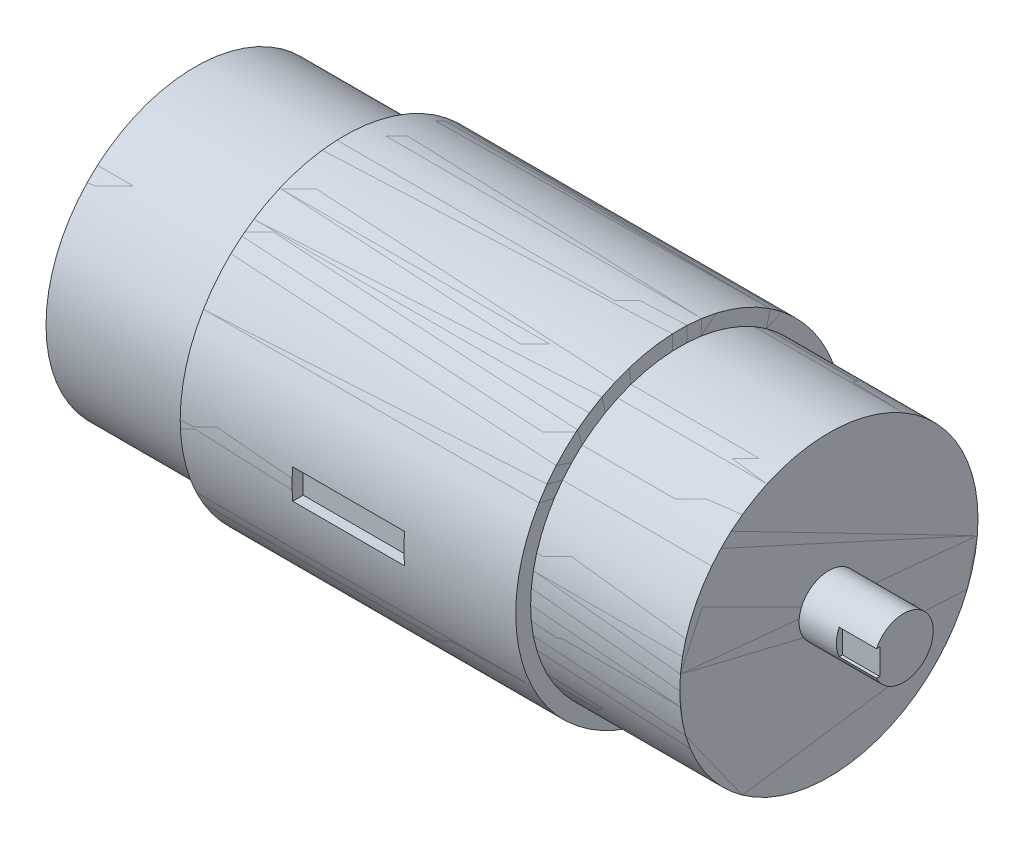
SolidWorks part; units mm, degrees
material "Cast Alloy Steel"
ref_plane "Front Plane" through (0, 0, 0) normal (0, 0, 1) x (1, 0, 0)
ref_plane "Top Plane" through (0, 0, 0) normal (0, 1, 0) x (1, 0, 0)
ref_plane "Right Plane" through (0, 0, 0) normal (1, 0, 0) x (0, 0, -1)
ref_plane "Plane1" through (800, 0, 0) normal (1, 0, 0) x (0, 0, -1)
sketch "Sketch3" plane through (800, 0, 0) normal (1, 0, 0) x (0, 0, -1)
  circle A0 centre (0, 0) radius 200
ref_plane "Plane2" through (200, 0, 0) normal (1, 0, 0) x (0, 0, -1)
ref_plane "Plane3" through (600, 0, 0) normal (1, 0, 0) x (0, 0, -1)
sketch "Sketch5" plane through (600, 0, 0) normal (1, 0, 0) x (0, 0, -1)
  circle A0 centre (0, 0) radius 220
  point P3 (-220, 0)
extrude "Boss-Extrude2" add sketch "Sketch3" against normal blind 200 contours A0
ref_plane "Plane4" through (800, 0, 0) normal (1, 0, 0) x (0, 0, -1)
sketch "Sketch6" plane through (800, 0, 0) normal (1, 0, 0) x (0, 0, -1)
  circle A0 centre (0, 0) radius 40
extrude "Boss-Extrude5" add sketch "Sketch6" along normal blind 100 separate body
ref_plane "Plane6" through (900, 0, 0) normal (1, 0, 0) x (0, 0, -1)
sketch "Sketch8" plane through (900, 0, 0) normal (1, 0, 0) x (0, 0, -1)
  line L3 (-36.1198, 17.186) -> (-31.7093, 17.186)
  line L5 (-31.7093, -17.186) -> (-36.1198, -17.186)
  line L6 (-31.7093, 17.186) -> (-31.7093, -17.186)
  arc A0 (-36.1198, 17.186) -> (-36.1198, -17.186) centre (0, 0) ccw
extrude "Cut-Extrude1" cut sketch "Sketch8" against normal blind 50
extrude "Boss-Extrude6" add sketch "Sketch5" against normal blind 450 contours A0
ref_plane "Plane7" through (150, 0, 0) normal (-1, 0, 0) x (0, 0, 1)
sketch "Sketch9" plane through (150, 0, 0) normal (-1, 0, 0) x (0, 0, 1)
  circle A0 centre (0, 0) radius 200
extrude "Boss-Extrude7" add sketch "Sketch9" along normal blind 200 contours A0
ref_plane "Plane8" through (600, 0, 220) normal (0, 0, 1) x (1, 0, 0)
sketch "Sketch10" plane through (600, 0, 220) normal (0, 0, 1) x (1, 0, 0)
  line L3 (-300, -20) -> (-150, -20)
  line L4 (-300, -20) -> (-300, 20)
  line L5 (-300, 20) -> (-150, 20)
  line L6 (-150, -20) -> (-150, 20)
  line L7 (-300, -20) -> (-150, 20) construction
  line L8 (-300, 20) -> (-150, -20) construction
  point P5 (-225, 0)
  point P6 (-225, 0)
extrude "Cut-Extrude2" cut sketch "Sketch10" against normal blind 15 contours L5 L6 L3 L4
surface "Surface-Knit1"
